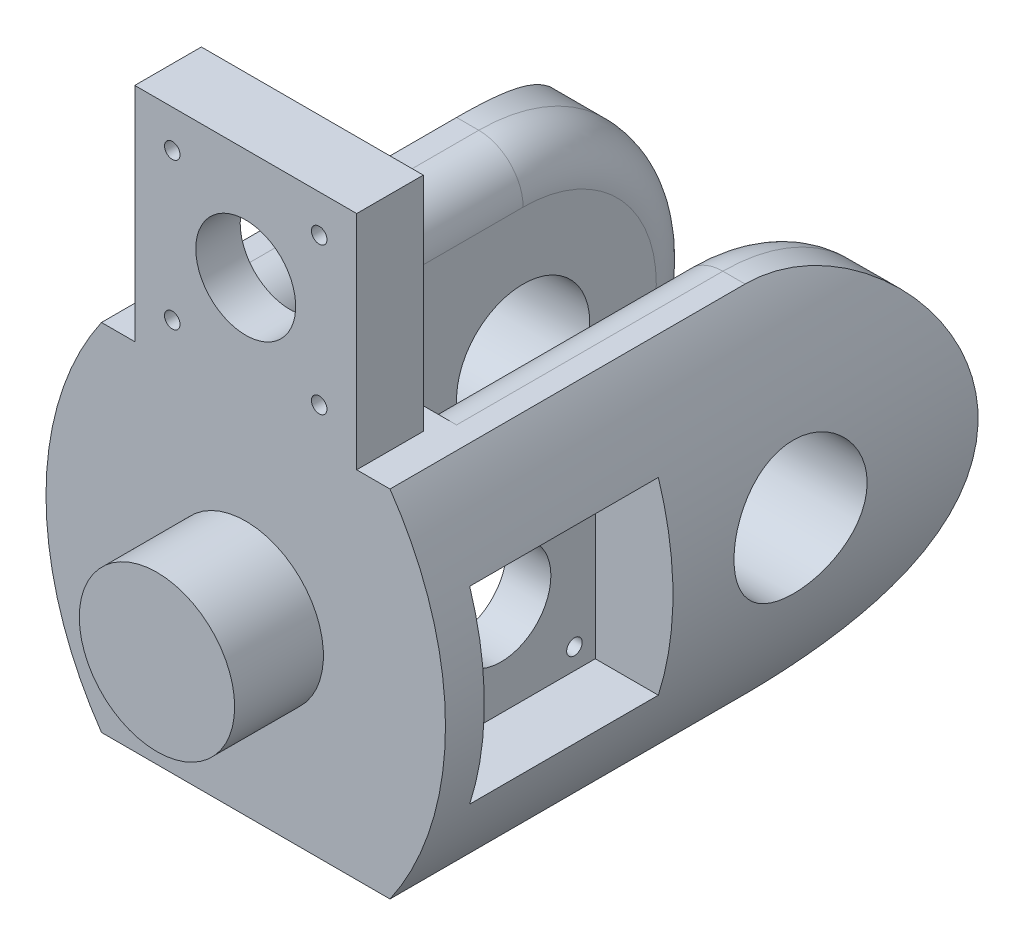
SolidWorks part; units mm, degrees
ref_plane "Front Plane" through (0, 0, 0) normal (0, 0, 1) x (1, 0, 0)
ref_plane "Top Plane" through (0, 0, 0) normal (0, 1, 0) x (1, 0, 0)
ref_plane "Right Plane" through (0, 0, 0) normal (1, 0, 0) x (0, 0, -1)
sketch "Sketch1" plane through (0, 0, 0) normal (0, 0, 1) x (1, 0, 0)
  line L0 (17.5, 0) -> (-17.5, 0) construction
  line L1 (-17.5, -40) -> (-17.5, 40)
  line L2 (-17.5, 40) -> (-32.5, 40)
  line L3 (-32.5, 40) -> (-32.5, -40) construction
  line L4 (-32.5, -40) -> (-17.5, -40)
  line L5 (17.5, -40) -> (17.5, 40)
  line L10 (17.5, 40) -> (32.5, 40)
  line L11 (32.5, 40) -> (32.5, -40) construction
  line L12 (32.5, -40) -> (17.5, -40)
  arc A0 (-32.5, -40) -> (-32.5, 40) centre (25.25, 0) cw
  arc A1 (32.5, 40) -> (32.5, -40) centre (-25.25, 0) cw
  point P4 (0, 0)
  point P7 (-17.5, 0)
  point P12 (17.5, 0)
  point P16 (-45, 0)
  point P17 (-32.5, 0)
  point P18 (32.5, 0)
  point P19 (45, 0)
  dimension "D1" = 35
  dimension "D2" = 80
  dimension "D3" = 15
  dimension "D4" = 15
  dimension "D5" = 12.5
  dimension "D6" = 12.5
extrude "Boss-Extrude1" add sketch "Sketch1" along normal blind 100
sketch "Sketch2" plane through (0, 0, 100) normal (0, 0, 1) x (1, 0, 0)
  line L0 (-32.5, 40) -> (32.5, 40)
  line L1 (-32.5, -40) -> (32.5, -40)
  arc A0 (-32.5, -40) -> (-32.5, 40) centre (25.25, 0) cw
  arc A1 (32.5, 40) -> (32.5, -40) centre (-25.25, 0) cw
extrude "Boss-Extrude2" add sketch "Sketch2" along normal blind 20
sketch "Sketch3" plane through (0, 0, 0) normal (1, 0, 0) x (0, 0, -1)
  line L0 (0, 0) -> (-80, 0) construction
  line L1 (-80, 0) -> (-100, 0) construction
  line L2 (0, 0) -> (0, 40)
  line L3 (0, 40) -> (-40, 40)
  line L4 (0, 0) -> (0, -40)
  line L5 (0, -40) -> (-40, -40)
  line L7 (-73.45, 16.55) -> (-106.55, 16.55) construction
  line L8 (-73.45, 16.55) -> (-73.45, -16.55) construction
  line L9 (-73.45, -16.55) -> (-106.55, -16.55) construction
  line L10 (-106.55, 16.55) -> (-106.55, -16.55) construction
  line L11 (-73.45, 16.55) -> (-106.55, -16.55) construction
  line L12 (-73.45, -16.55) -> (-106.55, 16.55) construction
  arc A0 (-40, -40) -> (-40, 40) centre (-40, 0) ccw
  circle A1 centre (-90, 0) radius 11.25
  circle A2 centre (-40, 0) radius 15
  circle A3 centre (-106.55, 16.55) radius 1.75
  circle A4 centre (-73.45, 16.55) radius 1.75
  circle A5 centre (-73.45, -16.55) radius 1.75
  circle A6 centre (-106.55, -16.55) radius 1.75
  dimension "D3" = 22.5
  dimension "D4" = 30
  dimension "D7" = 3.5
  dimension "D1" = 80
  dimension "D2" = 20
  dimension "D5" = 33.1
  dimension "D6" = 33.1
extrude "Cut-Extrude1" cut sketch "Sketch3" against normal through all both and the other way through all contours A0 L2 L3 | A0 L5 L4 | A2 | A1 | A5 | A4 | A3 | A6
ref_plane "Plane1" through (45, 0, 0) normal (1, 0, 0) x (0, 0, -1)
sketch "Sketch4" plane through (45, 0, 0) normal (1, 0, 0) x (0, 0, -1)
  line L1 (-68.75, -21.25) -> (-111.25, -21.25)
  line L2 (-68.75, -21.25) -> (-68.75, 21.25)
  line L3 (-68.75, 21.25) -> (-111.25, 21.25)
  line L4 (-111.25, -21.25) -> (-111.25, 21.25)
  line L5 (-68.75, -21.25) -> (-111.25, 21.25) construction
  line L6 (-68.75, 21.25) -> (-111.25, -21.25) construction
  point P0 (-90, 0)
  dimension "D1" = 42.5
  dimension "D2" = 42.5
extrude "Cut-Extrude2" cut sketch "Sketch4" against normal blind 17.5
ref_plane "Plane2" through (-45, 0, 0) normal (1, 0, 0) x (0, 0, -1)
sketch "Sketch5" plane through (-45, 0, 0) normal (1, 0, 0) x (0, 0, -1)
  line L1 (-111.25, -21.25) -> (-68.75, -21.25)
  line L2 (-111.25, -21.25) -> (-111.25, 21.25)
  line L3 (-111.25, 21.25) -> (-68.75, 21.25)
  line L4 (-68.75, -21.25) -> (-68.75, 21.25)
  line L5 (-111.25, -21.25) -> (-68.75, 21.25) construction
  line L6 (-111.25, 21.25) -> (-68.75, -21.25) construction
  point P0 (-90, 0)
  dimension "D1" = 42.5
  dimension "D2" = 42.5
extrude "Cut-Extrude4" cut sketch "Sketch5" along normal blind 17.5
sketch "Sketch6" plane through (0, 40, 0) normal (0, 1, 0) x (1, 0, 0)
  line L0 (0, -120) -> (0, -105) construction
  line L1 (32.5, -120) -> (-32.5, -120) construction
  line L2 (25, -105) -> (-25, -105)
  line L3 (-25, -105) -> (-25, -120)
  line L4 (-25, -120) -> (25, -120)
  line L5 (25, -120) -> (25, -105)
  point P7 (0, -105)
  dimension "D1" = 15
  dimension "D2" = 50
extrude "Boss-Extrude3" add sketch "Sketch6" along normal blind 50
sketch "Sketch7" plane through (0, 0, 105) normal (0, 0, -1) x (-1, 0, 0)
  line L0 (-25, 90) -> (25, 40) construction
  line L2 (16.55, 48.45) -> (-16.55, 48.45) construction
  line L3 (16.55, 48.45) -> (16.55, 81.55) construction
  line L4 (16.55, 81.55) -> (-16.55, 81.55) construction
  line L5 (-16.55, 48.45) -> (-16.55, 81.55) construction
  line L6 (16.55, 48.45) -> (-16.55, 81.55) construction
  line L7 (16.55, 81.55) -> (-16.55, 48.45) construction
  circle A0 centre (0, 65) radius 11.25
  circle A1 centre (16.55, 81.55) radius 1.75
  circle A2 centre (-16.55, 81.55) radius 1.75
  circle A3 centre (-16.55, 48.45) radius 1.75
  circle A4 centre (16.55, 48.45) radius 1.75
  point P4 (0, 65)
  dimension "D2" = 3.5
  dimension "D3" = 22.5
  dimension "D1" = 33.1
extrude "Cut-Extrude5" cut sketch "Sketch7" against normal through all both and the other way through all
sketch "Sketch8" plane through (0, 0, 105) normal (0, 0, -1) x (-1, 0, 0)
  line L1 (21.25, 43.75) -> (-21.25, 43.75)
  line L2 (21.25, 43.75) -> (21.25, 86.25)
  line L3 (21.25, 86.25) -> (-21.25, 86.25)
  line L4 (-21.25, 43.75) -> (-21.25, 86.25)
  line L5 (21.25, 43.75) -> (-21.25, 86.25) construction
  line L6 (21.25, 86.25) -> (-21.25, 43.75) construction
  point P0 (0, 65)
  dimension "D1" = 42.5
  dimension "D2" = 42.5
extrude "Cut-Extrude6" cut sketch "Sketch8" against normal blind 5
sketch "Sketch9" plane through (0, 0, 120) normal (0, 0, 1) x (1, 0, 0)
  circle A0 centre (0, 0) radius 17.5
  dimension "D1" = 35
extrude "Boss-Extrude4" add sketch "Sketch9" along normal blind 20
fillet "Fillet1" radius 10 6 edges at (-17.5, 40, 70) (-17.5, -40, 70) (17.5, -40, 70) (17.5, 40, 70) (-17.5, 0, 0) (17.5, 0, 0)
sketch "Sketch10" plane through (0, 0, 0) normal (1, 0, 0) x (0, 0, -1)
  line L0 (-106.55, 20.3) -> (-92.7033, 20.3)
  line L1 (-92.7033, 20.3) -> (-92.7033, 12.8)
  line L2 (-92.7033, 12.8) -> (-106.55, 12.8)
  line L3 (-106.55, -12.8) -> (-92.7033, -12.8)
  line L4 (-92.7033, -12.8) -> (-92.7033, -20.3)
  line L5 (-92.7033, -20.3) -> (-106.55, -20.3)
  arc A0 (-106.55, 20.3) -> (-106.55, 12.8) centre (-106.55, 16.55) ccw
  arc A1 (-106.55, -12.8) -> (-106.55, -20.3) centre (-106.55, -16.55) ccw
  dimension "D1" = 7.5
  dimension "D2" = 7.5
extrude "Cut-Extrude7" cut sketch "Sketch10" against normal blind 17.5 and the other way blind 17.5
